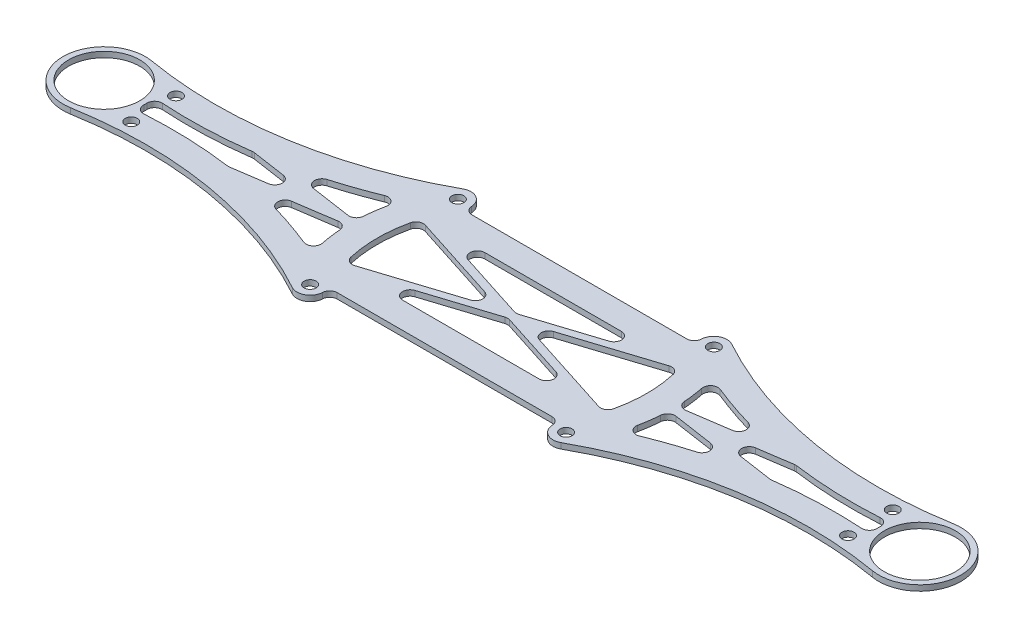
SolidWorks part; units mm, degrees
material "Thornel Mat VMA"
ref_plane "Front Plane" through (0, 0, 0) normal (0, 0, 1) x (1, 0, 0)
ref_plane "Top Plane" through (0, 0, 0) normal (0, 1, 0) x (1, 0, 0)
ref_plane "Right Plane" through (0, 0, 0) normal (1, 0, 0) x (0, 0, -1)
sketch "Sketch1" plane through (0, 0, 0) normal (0, 1, 0) x (1, 0, 0)
  line L0 (0, 43) -> (0, -43) construction
  line L1 (0, 0) -> (-43, 0) construction
  line L2 (0, 0) -> (-37.2391, 21.5) construction
  line L3 (0, 0) -> (-37.2391, -21.5) construction
  line L4 (-31.1769, 18) -> (31.1769, 18)
  line L5 (31.1769, -18) -> (-31.1769, -18)
  arc A0 (-37.2391, 21.5) -> (-37.2391, -21.5) centre (0, 0) ccw
  arc A1 (-31.1769, 18) -> (-31.1769, -18) centre (0, 0) ccw
  arc A2 (-107.1267, 10.8393) -> (-107.1267, -10.8393) centre (-109, 0) ccw
  circle A3 centre (-34.208, 19.75) radius 3.5
  circle A4 centre (-34.208, -19.75) radius 3.5
  arc A5 (-107.1267, 10.8393) -> (-35.8991, 22.8144) centre (-88.564, 118.2471) ccw
  arc A6 (-107.1267, -10.8393) -> (-35.8991, -22.8144) centre (-88.564, -118.2471) cw
  arc A7 (107.1267, -10.8393) -> (35.8991, -22.8144) centre (88.564, -118.2471) ccw
  arc A8 (107.1267, 10.8393) -> (35.8991, 22.8144) centre (88.564, 118.2471) cw
  circle A9 centre (34.208, -19.75) radius 3.5
  circle A10 centre (34.208, 19.75) radius 3.5
  arc A11 (107.1267, 10.8393) -> (107.1267, -10.8393) centre (109, 0) cw
  arc A12 (31.1769, 18) -> (31.1769, -18) centre (0, 0) cw
  arc A13 (37.2391, 21.5) -> (37.2391, -21.5) centre (0, 0) cw
  dimension "D1" = 86
  dimension "D2" = 7
  dimension "D3" = 22
  dimension "D4" = 109
  dimension "D5" = 0
  dimension "D8" = 109
  dimension "D6" = 30
  dimension "D7" = 30
  dimension "D9" = 36
extrude "Boss-Extrude1" add sketch "Sketch1" along normal mid plane 1.5 contours A2 A6 A4 A0 A3 A5 | A4 A1 A3 A0 | A4 | A3 | A12 L4 A1 L5 | A10 | A13 A10 A12 A9 | A9 | A10 A13 A9 A7 A11 A8
hole_wizard "Ø3.2 (3.2) Diameter Hole1" positions "Sketch3" profile "Sketch2" hole size "Ø3.2" standard "ANSI Metric" end condition through all
sketch "Sketch3" plane through (0, 0.75, 0) normal (0, 1, 0) x (1, 0, 0)
  circle A0 centre (-109, 0) radius 11
  circle A1 centre (109, 0) radius 11
  circle A2 centre (-95.7903, 5.9794) radius 3.5
  circle A3 centre (-95.7903, -5.9794) radius 3.5
  arc A4 (-107.1267, 10.8393) -> (-35.8991, 22.8144) centre (-88.564, 118.2471) ccw construction
  arc A5 (-35.8991, -22.8144) -> (-107.1267, -10.8393) centre (-88.564, -118.2471) ccw construction
  circle A6 centre (95.7903, 5.9794) radius 3.5
  circle A7 centre (95.7903, -5.9794) radius 3.5
  arc A8 (107.1267, -10.8393) -> (35.8991, -22.8144) centre (88.564, -118.2471) ccw construction
  arc A9 (35.8991, 22.8144) -> (107.1267, 10.8393) centre (88.564, 118.2471) ccw construction
  point P0 (-34.208, 19.75)
  point P3 (-34.208, -19.75)
  point P6 (34.208, -19.75)
  point P9 (34.208, 19.75)
  point P20 (-95.7903, 5.9794)
  point P22 (-95.7903, -5.9794)
  point P36 (95.7903, 5.9794)
  point P38 (95.7903, -5.9794)
  dimension "D1" = 7
sketch "Sketch2" plane through (-34.208, 0.75, -19.75) normal (1, 0, 0) x (0, 0, 1)
  line L0 (0, 0) -> (0, 1.5)
  line L1 (0, 1.5) -> (1.6, 1.5)
  line L2 (1.6, 1.5) -> (1.6, 0)
  line L5 (1.6, 0) -> (0, 0)
  line L11 (0, -6.35) -> (0, 107.95) construction
  dimension "Thru Hole Dia." = 3.2
  dimension "Thru Hole Depth" = 1.5
sketch "Sketch4" plane through (0, 0.75, 0) normal (0, 1, 0) x (1, 0, 0)
  line L0 (0, 18) -> (0, -18) construction
  line L1 (-31.1769, 18) -> (31.1769, 18) construction
  line L2 (31.1769, -18) -> (-31.1769, -18) construction
  line L3 (-43, 0) -> (-69.1391, -3.8851)
  line L4 (-43, 0) -> (-69.1391, 3.8851)
  line L7 (-42.853, 0.9891) -> (-68.9921, 4.8742)
  line L8 (-42.853, -0.9891) -> (-68.9921, -4.8742)
  line L9 (-43.147, 0.9891) -> (-72.4693, -3.369)
  line L10 (-43.147, -0.9891) -> (-72.4693, 3.369)
  line L11 (-43.147, -0.9891) -> (-69.2861, 2.8959) construction
  line L12 (-43.147, 0.9891) -> (-69.2861, -2.8959) construction
  line L13 (43.147, -0.9891) -> (72.4693, 3.369)
  line L14 (43.147, 0.9891) -> (72.4693, -3.369)
  line L15 (42.853, -0.9891) -> (68.9921, -4.8742)
  line L16 (42.853, 0.9891) -> (68.9921, 4.8742)
  line L17 (43, 0) -> (69.1391, 3.8851)
  line L18 (43, 0) -> (69.1391, -3.8851)
  circle A0 centre (-109, 0) radius 9.5
  arc A1 (-41.184, 12.3644) -> (-41.184, -12.3644) centre (0, 0) ccw
  arc A4 (-108.3188, 3.9416) -> (-32.5169, 16.6856) centre (-88.564, 118.2471) ccw
  arc A5 (-98.3261, 2.6586) -> (-41.184, 12.3644) centre (-88.564, 118.2471) ccw
  arc A6 (-98.3261, -2.6586) -> (-98.3261, 2.6586) centre (-109, 0) ccw
  arc A7 (-32.5169, -16.6856) -> (-108.3188, -3.9416) centre (-88.564, -118.2471) ccw
  arc A8 (-41.184, -12.3644) -> (-98.3261, -2.6586) centre (-88.564, -118.2471) ccw
  arc A19 (41.184, -12.3644) -> (98.3261, -2.6586) centre (88.564, -118.2471) cw
  arc A20 (98.3261, -2.6586) -> (98.3261, 2.6586) centre (109, 0) cw
  arc A21 (98.3261, 2.6586) -> (41.184, 12.3644) centre (88.564, 118.2471) cw
  arc A22 (41.184, 12.3644) -> (41.184, -12.3644) centre (0, 0) cw
  circle A23 centre (109, 0) radius 9.5
  dimension "D1" = 19
  dimension "D2" = 86
  dimension "D3" = 7
  dimension "D4" = 7
  dimension "D5" = 1
  dimension "D6" = 1
  dimension "D7" = 1
  dimension "D8" = 1
extrude "Cut-Extrude1" cut sketch "Sketch4" against normal through all contours A0 | A8 L9 L10 A5 A6 | A5 L7 A1 | A8 A1 L8 | A20 A21 L13 L14 A19 | A21 A22 L16 | L15 A22 A19 | A23
sketch "Sketch5" plane through (0, 0.75, 0) normal (0, 1, 0) x (1, 0, 0)
  line L2 (-31.1769, 11) -> (31.1769, 11)
  line L3 (-34.2783, 11) -> (34.2783, 11)
  line L4 (-34.2783, -11) -> (34.2783, 11)
  line L5 (31.1769, -11) -> (-31.1769, -11)
  line L6 (34.2783, -11) -> (-34.2783, -11)
  line L7 (34.2783, -11) -> (-34.2783, 11)
  line L8 (34.5838, -10.0478) -> (-33.9727, 11.9522)
  line L9 (33.9727, -11.9522) -> (-34.5838, 10.0478)
  line L10 (-34.5838, -10.0478) -> (33.9727, 11.9522)
  line L11 (-33.9727, -11.9522) -> (34.5838, 10.0478)
  arc A0 (-33.9595, 11.9479) -> (-33.9595, -11.9479) centre (0, 0) ccw
  arc A1 (33.9595, -11.9479) -> (33.9595, 11.9479) centre (0, 0) ccw
  dimension "D1" = 7
  dimension "D2" = 7
  dimension "D3" = 1
  dimension "D4" = 1
  dimension "D5" = 1
  dimension "D6" = 1
extrude "Cut-Extrude4" cut sketch "Sketch5" against normal through all contours L9 A0 L10 | L8 A1 L11 | L8 L10 L3 | L11 L6 L9
fillet "Fillet1" radius 2 38 edges at (49.802, 0, 0) (-31.1769, 0, 18) (-31.1769, 0, -18) (31.1769, 0, -18) (31.1769, 0, 18) (41.184, 0, -12.3644) (42.9882, 0, -1.0092) (42.9882, 0, 1.0092) (41.184, 0, 12.3644) (66.0961, 0, 4.4438) (72.4693, 0, 3.369) (72.4693, 0, -3.369) (98.3261, 0, -2.6586) (98.3261, 0, 2.6586) (66.0961, 0, -4.4438) (31.0055, 0, 11) (34.5706, 0, 10.0436) (31.0055, 0, -11) (34.5706, 0, -10.0436) (0, 0, 1.0502) (-3.2727, 0, 0) (3.2727, 0, 0) (-31.0055, 0, -11) (-34.5706, 0, -10.0436) (-31.0055, 0, 11) (0, 0, -1.0502) (-34.5706, 0, 10.0436) (-66.0961, 0, 4.4438) (-66.0961, 0, -4.4438) (-41.184, 0, -12.3644) (-42.9882, 0, 1.0092) (-49.802, 0, 0) (-41.184, 0, 12.3644) (-42.9882, 0, -1.0092) (-72.4693, 0, 3.369) (-72.4693, 0, -3.369) (-98.3261, 0, -2.6586) (-98.3261, 0, 2.6586)
